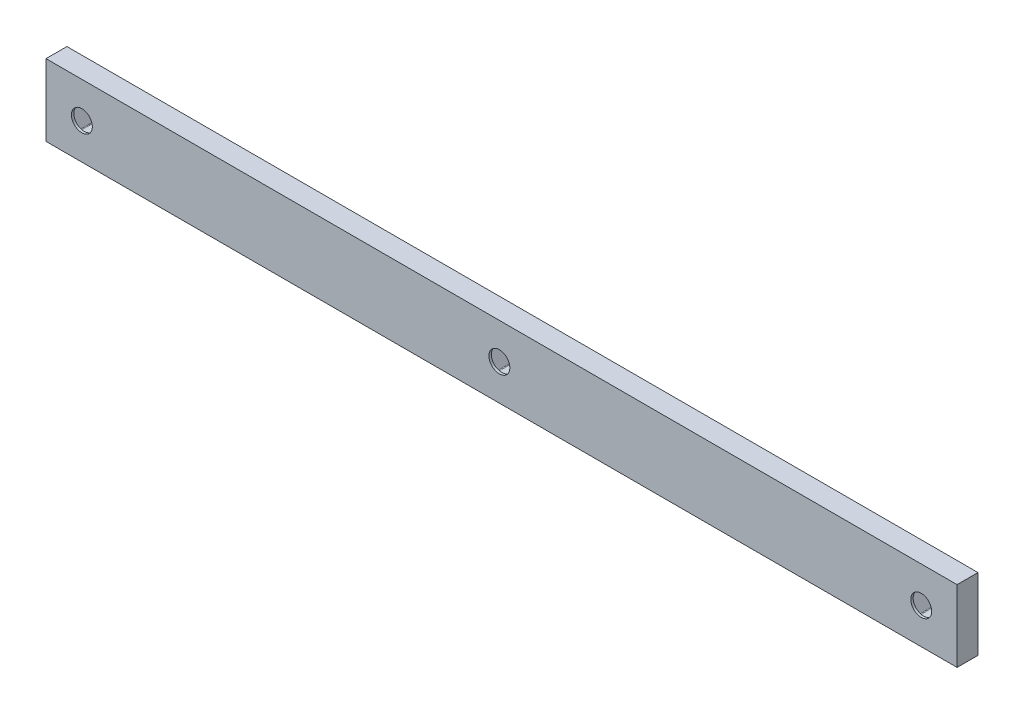
SolidWorks part; units mm, degrees
ref_plane "Front Plane" through (0, 0, 0) normal (0, 0, 1) x (1, 0, 0)
ref_plane "Top Plane" through (0, 0, 0) normal (0, 1, 0) x (1, 0, 0)
ref_plane "Right Plane" through (0, 0, 0) normal (1, 0, 0) x (0, 0, -1)
ref_plane "Plane1" through (0, 0, 0) normal (0, 0, -1) x (-1, 0, 0)
sketch "Sketch1" plane through (0, 0, 0) normal (0, 0, -1) x (-1, 0, 0)
  line L0 (91.8503, -6) -> (91.8503, 6)
  line L1 (91.8503, 6) -> (-60.5711, 6)
  line L2 (-60.5711, 6) -> (-60.5711, -6)
  line L3 (-60.5711, -6) -> (91.8503, -6)
extrude "Boss-Extrude1" add sketch "Sketch1" against normal blind 3.5
sketch "Sketch2" plane through (0, 0, 0) normal (0, 0, -1) x (-1, 0, 0)
  line L0 (17.6743, -2.9) -> (19.3486, 0)
  line L1 (19.3486, 0) -> (17.6743, 2.9)
  line L2 (17.6743, 2.9) -> (14.3257, 2.9)
  line L3 (14.3257, 2.9) -> (12.6514, 0)
  line L4 (12.6514, 0) -> (14.3257, -2.9)
  line L5 (14.3257, -2.9) -> (17.6743, -2.9)
extrude "Cut-Extrude1" cut sketch "Sketch2" against normal blind 3.1
sketch "Sketch3" plane through (0, 0, 0) normal (0, 0, -1) x (-1, 0, 0)
  line L0 (-57.9197, 0) -> (-56.2454, -2.9)
  line L1 (-56.2454, -2.9) -> (-52.8967, -2.9)
  line L2 (-52.8967, -2.9) -> (-51.2224, 0)
  line L3 (-51.2224, 0) -> (-52.8967, 2.9)
  line L4 (-52.8967, 2.9) -> (-56.2454, 2.9)
  line L5 (-56.2454, 2.9) -> (-57.9197, 0)
extrude "Cut-Extrude2" cut sketch "Sketch3" against normal blind 3.1
sketch "Sketch4" plane through (0, 0, 0) normal (0, 0, -1) x (-1, 0, 0)
  line L0 (82.5017, 0) -> (84.176, -2.9)
  line L1 (84.176, -2.9) -> (87.5246, -2.9)
  line L2 (87.5246, -2.9) -> (89.199, 0)
  line L3 (89.199, 0) -> (87.5246, 2.9)
  line L4 (87.5246, 2.9) -> (84.176, 2.9)
  line L5 (84.176, 2.9) -> (82.5017, 0)
extrude "Cut-Extrude3" cut sketch "Sketch4" against normal blind 3.1
hole_wizard "Ø3.5 (3.5) Diameter Hole1" positions "Sketch6" profile "Sketch5" hole size "Ø3.5" standard "ANSI Metric"
sketch "Sketch6" plane through (0, 0, 3.1) normal (0, 0, -1) x (-1, 0, 0)
  point P0 (-54.5711, 0)
  point P1 (85.8503, 0)
  point P2 (16, 0)
sketch "Sketch5" plane through (54.5711, 0, 3.1) normal (1, 0, 0) x (0, 1, 0)
  line L0 (0, 0) -> (0, 0.4)
  line L1 (0, 0.4) -> (1.75, 0.4)
  line L2 (1.75, 0.4) -> (1.75, 0)
  line L5 (1.75, 0) -> (0, 0)
  line L11 (0, -6.35) -> (0, 107.95) construction
  dimension "Thru Hole Dia." = 3.5
  dimension "Thru Hole Depth" = 0.4
fillet "Fillet1" radius 0.15 18 edges at (-87.5246, 2.9, 1.55) (52.8967, -2.9, 1.55) (52.8967, 2.9, 1.55) (-17.6743, -2.9, 1.55) (-82.5017, 0, 1.55) (-14.3257, -2.9, 1.55) (-87.5246, -2.9, 1.55) (-12.6514, 0, 1.55) (51.2224, 0, 1.55) (-14.3257, 2.9, 1.55) (-84.176, -2.9, 1.55) (-17.6743, 2.9, 1.55) (-84.176, 2.9, 1.55) (56.2454, -2.9, 1.55) (-89.199, 0, 1.55) (57.9197, 0, 1.55) (-19.3486, 0, 1.55) (56.2454, 2.9, 1.55)
sketch "Sketch7" plane through (0, 0, 0) normal (0, 0, -1) x (-1, 0, 0)
  point P0 (-54.5711, 0)
  point P1 (16, 0)
  point P3 (85.8503, 0)
